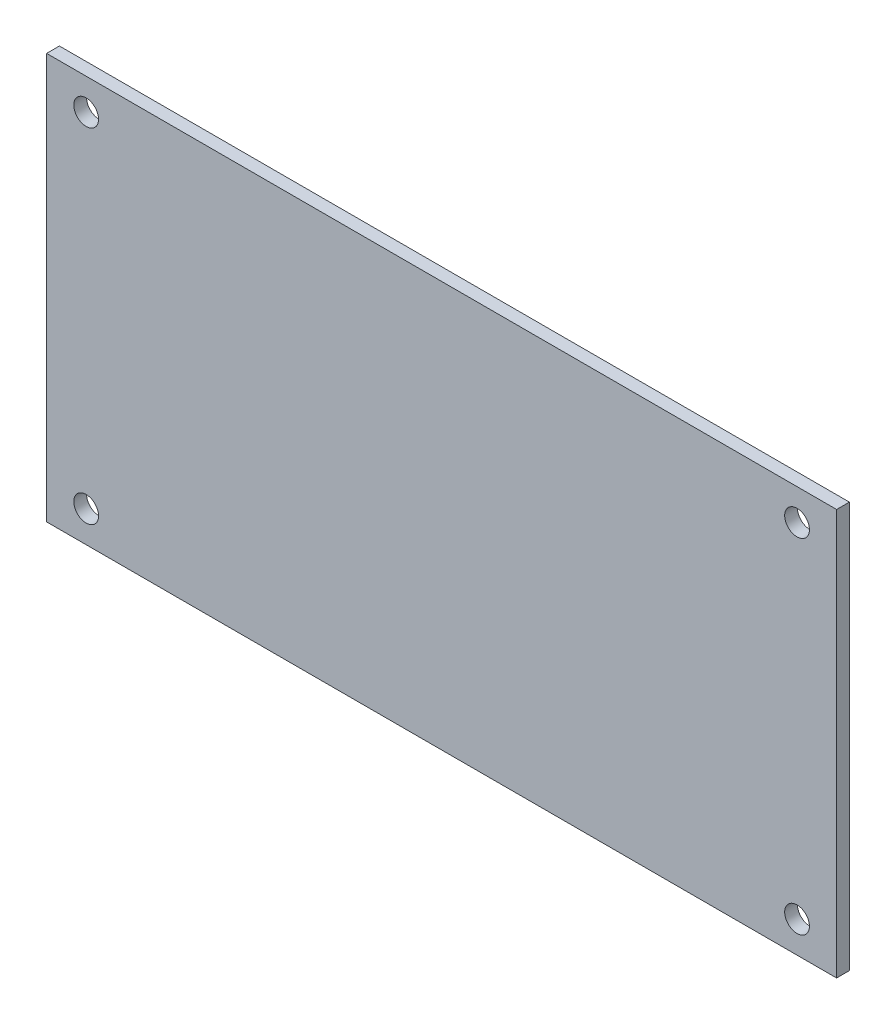
SolidWorks part; units mm, degrees
ref_plane "Front Plane" through (0, 0, 0) normal (0, 0, 1) x (1, 0, 0)
ref_plane "Top Plane" through (0, 0, 0) normal (0, 1, 0) x (1, 0, 0)
ref_plane "Right Plane" through (0, 0, 0) normal (1, 0, 0) x (0, 0, -1)
sketch "Sketch1" plane through (0, 0, 0) normal (0, 0, 1) x (1, 0, 0)
  line L0 (-49.45, -25.4) -> (49.45, -25.4)
  line L1 (-49.45, -25.4) -> (-49.45, 25.4)
  line L2 (49.45, -25.4) -> (49.45, 25.4)
  line L3 (-49.45, 25.4) -> (49.45, 25.4)
  line L4 (-49.45, -25.4) -> (49.45, 25.4) construction
  line L5 (49.45, -25.4) -> (-49.45, 25.4) construction
  line L6 (-44.5, -21.5) -> (44.5, -21.5) construction
  line L7 (-44.5, -21.5) -> (-44.5, 21.5) construction
  line L8 (44.5, -21.5) -> (44.5, 21.5) construction
  line L9 (-44.5, 21.5) -> (44.5, 21.5) construction
  line L10 (-44.5, -21.5) -> (44.5, 21.5) construction
  line L11 (44.5, -21.5) -> (-44.5, 21.5) construction
  circle A0 centre (-44.5, 21.5) radius 1.55
  circle A1 centre (44.5, 21.5) radius 1.55
  circle A2 centre (44.5, -21.5) radius 1.55
  circle A3 centre (-44.5, -21.5) radius 1.55
  point P1 (0, 0)
  point P2 (0, 0)
  dimension "D5" = 3.1
  dimension "D1" = 98.9
  dimension "D2" = 50.8
  dimension "D3" = 89
  dimension "D4" = 43
extrude "Boss-Extrude2" add sketch "Sketch1" along normal blind 1.6
